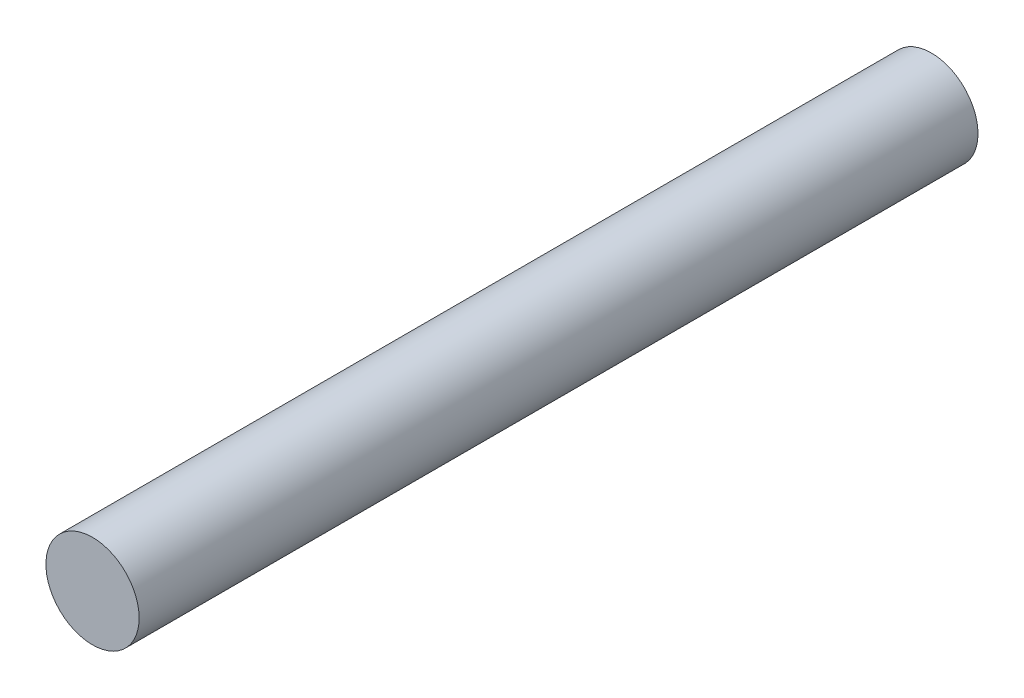
SolidWorks part; units mm, degrees
ref_plane "Piano frontale" through (0, 0, 0) normal (0, 0, 1) x (1, 0, 0)
ref_plane "Piano superiore" through (0, 0, 0) normal (0, 1, 0) x (1, 0, 0)
ref_plane "Piano destro" through (0, 0, 0) normal (1, 0, 0) x (0, 0, -1)
sketch "Schizzo1" plane through (0, 0, 0) normal (0, 0, 1) x (1, 0, 0)
  circle A0 centre (0, 0) radius 2.5
  dimension "D1" = 5
extrude "Estrusione-Estrusione1" add sketch "Schizzo1" along normal blind 45
